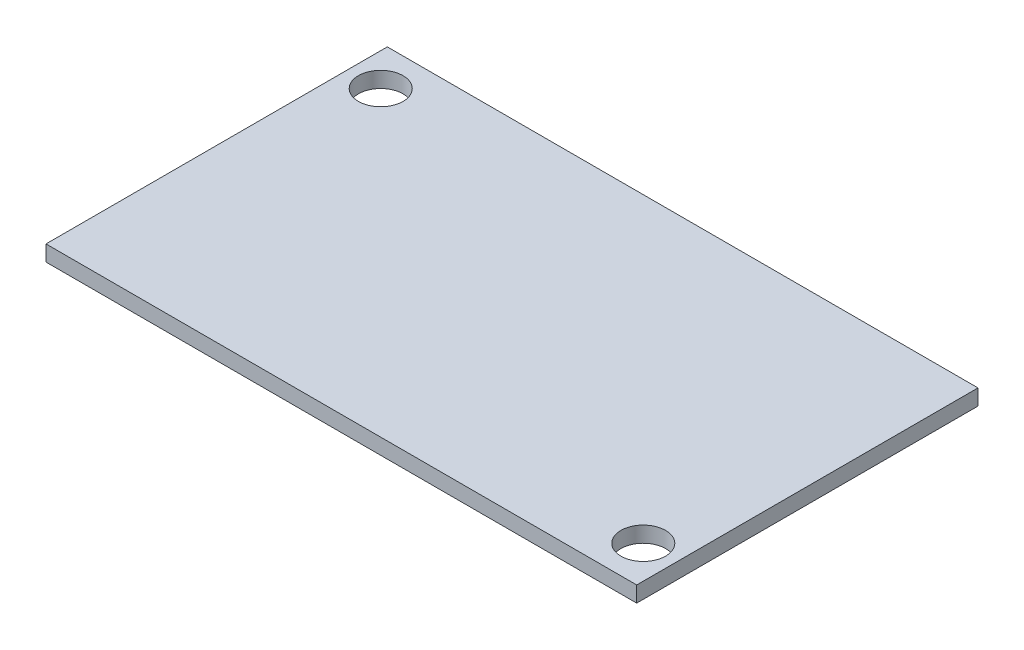
SolidWorks part; units mm, degrees
ref_plane "Front Plane" through (0, 0, 0) normal (0, 0, 1) x (1, 0, 0)
ref_plane "Top Plane" through (0, 0, 0) normal (0, 1, 0) x (1, 0, 0)
ref_plane "Right Plane" through (0, 0, 0) normal (1, 0, 0) x (0, 0, -1)
sketch "Sketch1" plane through (0, 0, 0) normal (0, 1, 0) x (1, 0, 0)
  line L1 (-24.7775, 1.3586) -> (20.2225, 1.3586)
  line L2 (-24.7775, 1.3586) -> (-24.7775, -24.6414)
  line L3 (-24.7775, -24.6414) -> (20.2225, -24.6414)
  line L4 (20.2225, 1.3586) -> (20.2225, -24.6414)
  dimension "D1" = 26
  dimension "D2" = 45
extrude "Boss-Extrude1" add sketch "Sketch1" along normal blind 1.2
hole_wizard "M3 Clearance Hole1" positions "3DSketch1" profile "Sketch2" hole size "M3" standard "ANSI Metric" end condition through all
sketch3d "3DSketch1"
  line L0 (-24.7775, 1.2, 24.6414) -> (20.2225, 1.2, 24.6414) construction
  line L1 (20.2225, 1.2, 24.6414) -> (20.2225, 1.2, -1.3586) construction
  line L2 (-24.7775, 1.2, -1.3586) -> (-24.7775, 1.2, 24.6414) construction
  line L3 (20.2225, 1.2, -1.3586) -> (-24.7775, 1.2, -1.3586) construction
  point P0 (-22.2775, 1.2, 1.6414)
  point P2 (17.7225, 1.2, 21.6414)
  dimension "D1" = 3
  dimension "D2" = 2.5
  dimension "D3" = 2.5
  dimension "D4" = 3
sketch "Sketch2" plane through (-22.2775, 1.2, 1.6414) normal (1, 0, 0) x (0, 0, 1)
  line L0 (0, 0) -> (0, 1.2)
  line L1 (0, 1.2) -> (1.7, 1.2)
  line L2 (1.7, 1.2) -> (1.7, 0)
  line L5 (1.7, 0) -> (0, 0)
  line L11 (0, -6.35) -> (0, 107.95) construction
  dimension "Thru Hole Dia." = 3.4
  dimension "Thru Hole Depth" = 1.2
